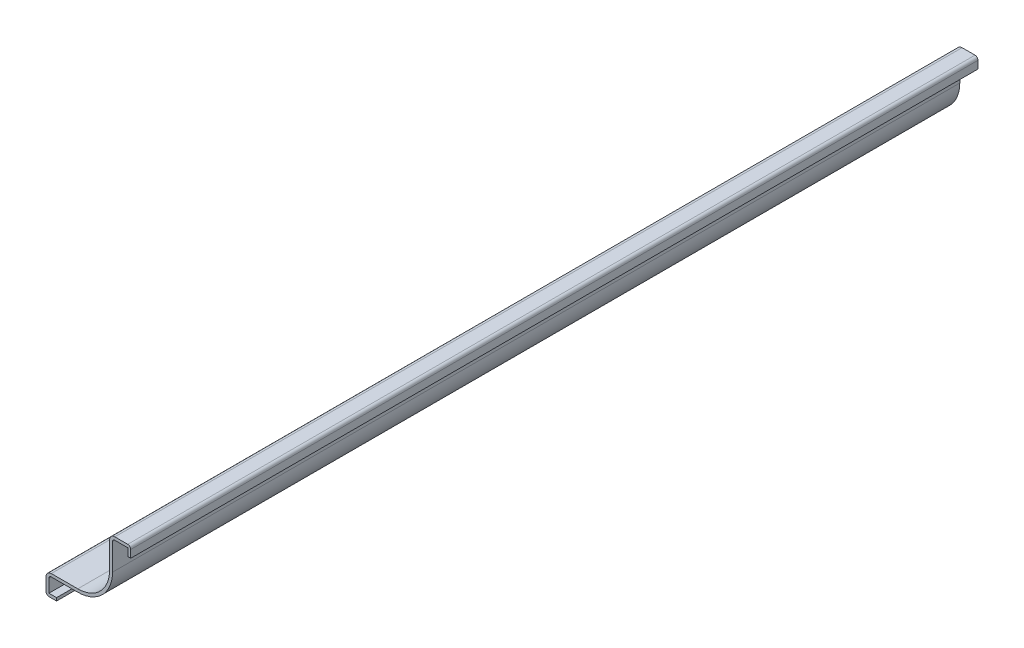
SolidWorks part; units mm, degrees
ref_plane "Front Plane" through (0, 0, 0) normal (0, 0, 1) x (1, 0, 0)
ref_plane "Top Plane" through (0, 0, 0) normal (0, 1, 0) x (1, 0, 0)
ref_plane "Right Plane" through (0, 0, 0) normal (1, 0, 0) x (0, 0, -1)
sketch "Sketch1" plane through (0, 0, 0) normal (0, 0, 1) x (1, 0, 0)
  line L0 (-22.225, 0) -> (0, 0) construction
  line L1 (0, 22.225) -> (0, 0) construction
  line L2 (-22.225, 0) -> (-25.4, 0)
  line L3 (-25.4, 0) -> (-25.4, 4.7625)
  line L4 (-23.8125, 6.35) -> (-15.875, 6.35)
  line L5 (-6.35, 15.875) -> (-6.35, 23.8125)
  line L6 (-4.7625, 25.4) -> (0, 25.4)
  line L7 (0, 25.4) -> (0, 22.225)
  arc A0 (-25.4, 4.7625) -> (-23.8125, 6.35) centre (-23.8125, 4.7625) cw
  arc A1 (-15.875, 6.35) -> (-6.35, 15.875) centre (-15.875, 15.875) ccw
  arc A2 (-6.35, 23.8125) -> (-4.7625, 25.4) centre (-4.7625, 23.8125) cw
  point P14 (-15.8712, 6.35)
  point P15 (-15.7015, 6.35)
  point P17 (0, 0)
  dimension "D5" = 1.5875
  dimension "D6" = 9.525
  dimension "D1" = 25.4
  dimension "D2" = 3.175
  dimension "D3" = 6.35
  dimension "D4" = 6.35
extrude "Extrude-Thin1" add sketch "Sketch1" against normal blind 254 thin
fillet "Fillet1" radius 0.889 2 edges at (-25.4, 0, -127) (0, 25.4, -127)
